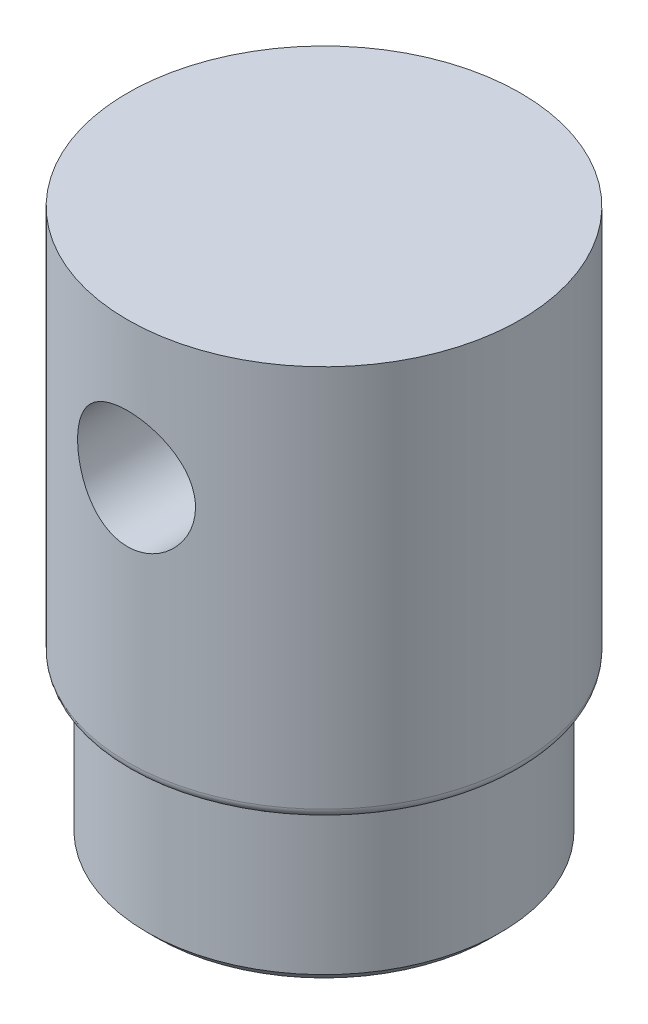
SolidWorks part; units mm, degrees
ref_plane "前视基准面" through (0, 0, 0) normal (0, 0, 1) x (1, 0, 0)
ref_plane "上视基准面" through (0, 0, 0) normal (0, 1, 0) x (1, 0, 0)
ref_plane "右视基准面" through (0, 0, 0) normal (1, 0, 0) x (0, 0, -1)
sketch "草图1" plane through (0, 0, 0) normal (0, 1, 0) x (1, 0, 0)
  circle A0 centre (0, 0) radius 10
  dimension "D1" = 20
extrude "凸台-拉伸1" add sketch "草图1" along normal blind 20
sketch "草图2" plane through (0, 0, 0) normal (0, -1, 0) x (1, 0, 0)
  circle A0 centre (0, 0) radius 9
  dimension "D1" = 18
extrude "凸台-拉伸2" add sketch "草图2" along normal blind 8
cosmetic thread "装饰螺纹线1" parameters "D2"=15.294
sketch "草图3" plane through (0, 0, 0) normal (0, 0, 1) x (1, 0, 0)
  line L0 (10, 20) -> (-10, 20) construction
  circle A0 centre (0, 13) radius 3
  dimension "D1" = 6
  dimension "D2" = 7
  dimension "D3" = 0
extrude "切除-拉伸1" cut sketch "草图3" against normal through all both and the other way through all
fillet "圆角1" radius 0.5 1 edges at (0, 0, 10)
chamfer "倒角1" distance 0.5 angle 45 1 edges at (0, -8, -9)
sketch "草图4" plane through (0, 0, 0) normal (0, 0, 1) x (1, 0, 0)
  line L0 (10, 0.5) -> (-10, 0.5) construction
  circle A0 centre (0, 13) radius 3
  dimension "D1" = 12.5
